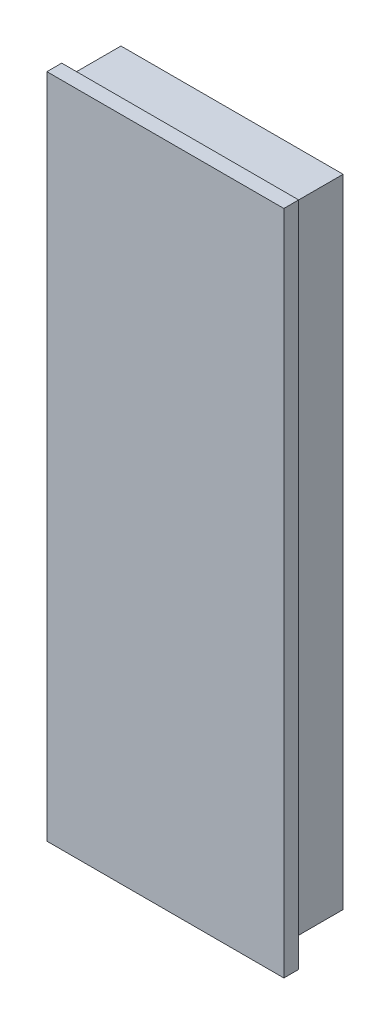
SolidWorks part; units mm, degrees
ref_plane "前视基准面" through (0, 0, 0) normal (0, 0, 1) x (1, 0, 0)
ref_plane "上视基准面" through (0, 0, 0) normal (0, 1, 0) x (1, 0, 0)
ref_plane "右视基准面" through (0, 0, 0) normal (1, 0, 0) x (0, 0, -1)
sketch "草图1" plane through (0, 0, 0) normal (0, 0, 1) x (1, 0, 0)
  line L1 (-7.5, 21.5) -> (7.5, 21.5)
  line L2 (-7.5, 21.5) -> (-7.5, -21.5)
  line L3 (-7.5, -21.5) -> (7.5, -21.5)
  line L4 (7.5, 21.5) -> (7.5, -21.5)
  line L5 (-7.5, 21.5) -> (7.5, -21.5) construction
  line L6 (-7.5, -21.5) -> (7.5, 21.5) construction
  point P0 (0, 0)
  dimension "D1" = 43
  dimension "D2" = 15
extrude "凸台-拉伸1" add sketch "草图1" along normal blind 4
sketch "草图2" plane through (0, 0, 4) normal (0, 0, 1) x (1, 0, 0)
  line L0 (-7.5, 21.5) -> (-7.5, -21.5) construction
  line L1 (-7.5, 22.5) -> (8.5, 22.5)
  line L2 (-7.5, 22.5) -> (-7.5, -22.5)
  line L3 (-7.5, -22.5) -> (8.5, -22.5)
  line L4 (8.5, 22.5) -> (8.5, -22.5)
  line L5 (7.5, 22.5) -> (7.5, 21.5) construction
  line L6 (7.5, 21.5) -> (8.5, 21.5) construction
  line L7 (-7.5, -21.5) -> (7.5, -21.5) construction
  dimension "D1" = 1
  dimension "D2" = 1
extrude "凸台-拉伸2" add sketch "草图2" along normal blind 1
